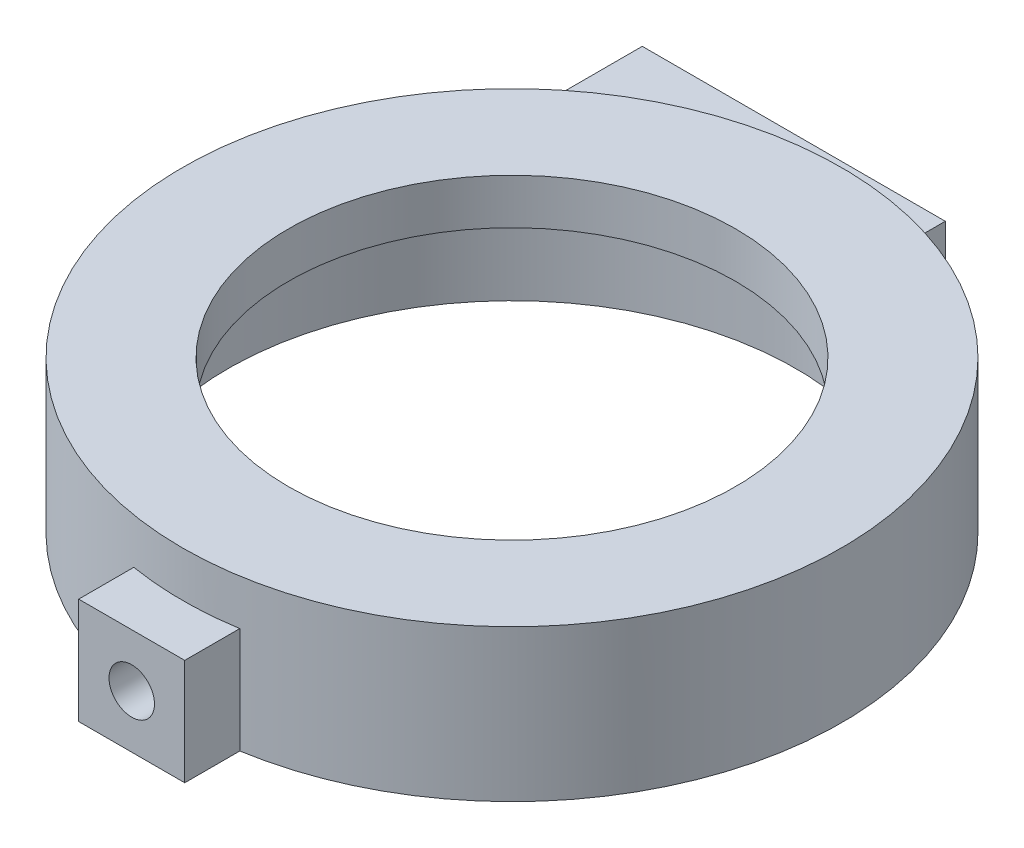
SolidWorks part; units mm, degrees
ref_plane "Front Plane" through (0, 0, 0) normal (0, 0, 1) x (1, 0, 0)
ref_plane "Top Plane" through (0, 0, 0) normal (0, 1, 0) x (1, 0, 0)
ref_plane "Right Plane" through (0, 0, 0) normal (1, 0, 0) x (0, 0, -1)
sketch "Sketch1" plane through (0, 0, 0) normal (0, 1, 0) x (1, 0, 0)
  line L0 (0, -20.1) -> (0, -25.1) construction
  line L1 (3.5, -25.1) -> (-3.5, -25.1)
  line L2 (-3.5, -25.1) -> (-3.5, -21.4665)
  line L3 (3.5, -25.1) -> (3.5, -21.4665)
  line L4 (0, 20.1) -> (0, 25.1) construction
  line L5 (3.5, 25.1) -> (-3.5, 25.1)
  line L6 (-3.5, 25.1) -> (-3.5, 21.4665)
  line L7 (3.5, 25.1) -> (3.5, 21.4665)
  circle A0 centre (0, 0) radius 18.75
  arc A1 (3.5, -21.4665) -> (3.5, 21.4665) centre (0, 0) ccw
  arc A2 (-3.5, 21.4665) -> (-3.5, -21.4665) centre (0, 0) ccw
  circle A3 centre (0, 0) radius 21.75 construction
  point P11 (19.2217, 5.8767)
  dimension "D1" = 3
  dimension "D3" = 3.5
  dimension "D2" = 5
  dimension "D4" = 5
  dimension "D5" = 3.5
extrude "Boss-Extrude1" add sketch "Sketch1" along normal blind 7 contours A1 L7 L5 L6 A2 L2 L1 L3 | A0
sketch "Sketch2" plane through (0, 0, 25.1) normal (0, 0, 1) x (1, 0, 0)
  line L0 (0, 7) -> (0, 0) construction
  line L1 (3.5, 7) -> (-3.5, 7) construction
  circle A0 centre (0, 3.5) radius 1.5
extrude "Cut-Extrude1" cut sketch "Sketch2" against normal blind 7
sketch "Sketch3" plane through (0, 0, -25.1) normal (0, 0, -1) x (-1, 0, 0)
  line L0 (0, 7) -> (0, 0) construction
  line L1 (-3.5, 7) -> (3.5, 7) construction
  circle A0 centre (0, 3.5) radius 1.4
extrude "Cut-Extrude2" cut sketch "Sketch3" against normal blind 5
sketch "Sketch6" plane through (0, 0, 0) normal (0, -1, 0) x (-1, 0, 0)
  line L0 (3.5, 25.1) -> (16.5, 25.1)
  line L1 (16.5, 25.1) -> (16.5, 14.1708)
  line L2 (3.5, 25.1) -> (3.5, 21.4665)
  arc A0 (3.5, -21.4665) -> (3.5, 21.4665) centre (0, 0) ccw construction
  arc A2 (16.5, 14.1708) -> (3.5, 21.4665) centre (0, 0) ccw
  dimension "D1" = 13
extrude "Boss-Extrude3" add sketch "Sketch6" against normal blind 7
sketch "Sketch7" plane through (0, 0, -25.1) normal (0, 0, -1) x (-1, 0, 0)
  line L0 (0, 3.5) -> (10, 3.5) construction
  circle A0 centre (10, 3.5) radius 1.4
  dimension "D1" = 10
extrude "Cut-Extrude3" cut sketch "Sketch7" against normal blind 7
sketch "Sketch9" plane through (0, 7, 0) normal (0, 1, 0) x (1, 0, 0)
  line L0 (0, -18.75) -> (0, -14.75) construction
  circle A0 centre (0, 0) radius 21.75
  circle A1 centre (0, 0) radius 18.75 construction
  circle A2 centre (0, 0) radius 14.75
extrude "Boss-Extrude5" add sketch "Sketch9" along normal blind 3 contours A0 | A2
